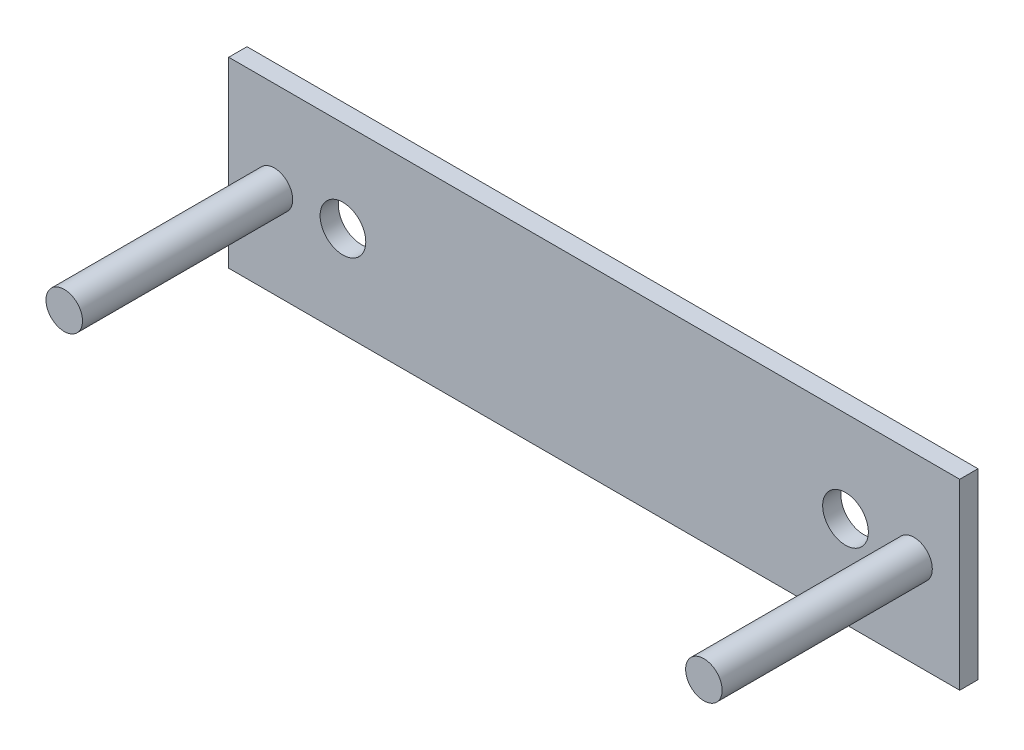
SolidWorks part; units mm, degrees
ref_plane "Front Plane" through (0, 0, 0) normal (0, 0, 1) x (1, 0, 0)
ref_plane "Top Plane" through (0, 0, 0) normal (0, 1, 0) x (1, 0, 0)
ref_plane "Right Plane" through (0, 0, 0) normal (1, 0, 0) x (0, 0, -1)
sketch "Sketch1" plane through (0, 0, 0) normal (0, 0, 1) x (1, 0, 0)
  line L1 (-49.9258, -6.3952) -> (30.0742, -6.3952)
  line L2 (-49.9258, -6.3952) -> (-49.9258, -26.3952)
  line L3 (-49.9258, -26.3952) -> (30.0742, -26.3952)
  line L4 (30.0742, -6.3952) -> (30.0742, -26.3952)
  circle A0 centre (-37.4258, -16.3952) radius 2.5
  circle A1 centre (17.5742, -16.3952) radius 2.5
extrude "Boss-Extrude1" add sketch "Sketch1" along normal blind 2
sketch "Sketch2" plane through (0, 0, 2) normal (0, 0, 1) x (1, 0, 0)
  circle A0 centre (25.0742, -16.3952) radius 2
  circle A1 centre (-44.9258, -16.3952) radius 2
extrude "Boss-Extrude2" add sketch "Sketch2" along normal blind 23
